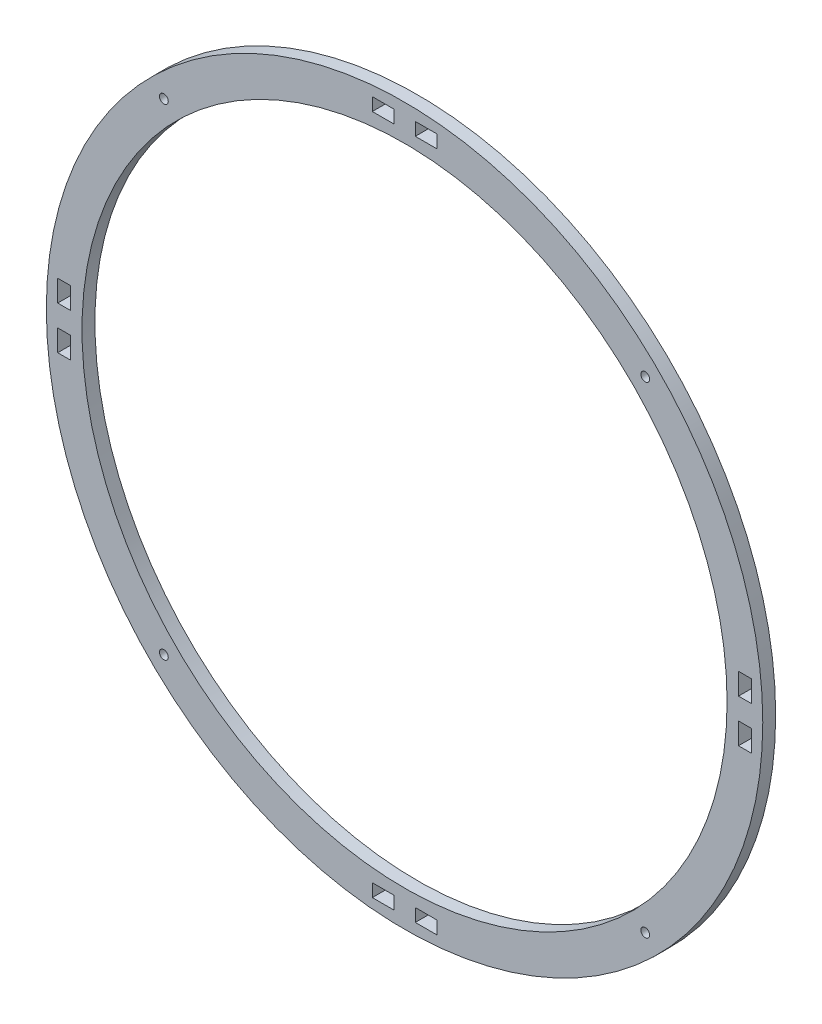
SolidWorks part; units mm, degrees
ref_plane "Alzado" through (0, 0, 0) normal (0, 0, 1) x (1, 0, 0)
ref_plane "Planta" through (0, 0, 0) normal (0, 1, 0) x (1, 0, 0)
ref_plane "Vista lateral" through (0, 0, 0) normal (1, 0, 0) x (0, 0, -1)
sketch "Croquis1" plane through (0, 0, 0) normal (0, 0, 1) x (1, 0, 0)
  line L0 (-44.7644, 42.1119) -> (355.2356, 42.1119)
  line L1 (355.2356, 42.1119) -> (355.2356, -357.8881)
  line L2 (355.2356, -357.8881) -> (-44.7644, -357.8881)
  line L3 (-44.7644, -357.8881) -> (-44.7644, 42.1119)
  line L4 (51.705, -49.341) -> (50.9394, -50.0625)
  circle A0 centre (154.1908, -158.8703) radius 150
  arc A1 (-0.0578, -95.9225) -> (308.4393, -95.9225) centre (154.1908, -158.8703) ccw
  arc A2 (267.7806, -36.9999) -> (40.601, -36.9999) centre (154.1908, -158.8703) ccw
  circle A3 centre (154.1908, -158.8703) radius 166.5985
  dimension "D1" = 400
  dimension "D2" = 400
extrude "Saliente-Extruir1" add sketch "Croquis1" along normal blind 6
sketch "Croquis2" plane through (0, 0, 6) normal (0, 0, 1) x (1, 0, 0)
  line L0 (154.1908, -8.8703) -> (154.1908, 7.7281)
  line L1 (154.1908, -308.8703) -> (154.1908, -325.4688)
  line L2 (304.1908, -158.8703) -> (320.7893, -158.8703)
  line L3 (4.1908, -158.8703) -> (-12.4077, -158.8703)
  line L4 (36.3879, -276.6733) -> (48.1248, -264.9364)
  line L5 (271.9937, -276.6733) -> (260.2568, -264.9364)
  line L6 (48.1248, -52.8043) -> (36.3879, -41.0674)
  line L7 (260.2568, -52.8043) -> (271.9937, -41.0674)
  line L8 (159.1908, 2.4289) -> (169.1908, 2.4289)
  line L9 (149.1908, 2.4289) -> (139.1908, 2.4289)
  line L10 (149.1908, -0.5711) -> (149.1908, 2.4289)
  line L11 (149.1908, -0.5711) -> (149.1908, -3.5711)
  line L12 (149.1908, -3.5711) -> (159.1908, -3.5711)
  line L13 (159.1908, -3.5711) -> (159.1908, 2.4289)
  line L14 (159.1908, 2.4289) -> (149.1908, 2.4289)
  line L15 (139.1908, 2.4289) -> (139.1908, -3.5711)
  line L16 (139.1908, -3.5711) -> (169.1908, -3.5711)
  line L17 (169.1908, -3.5711) -> (169.1908, 2.4289)
  line L18 (169.1908, -314.1696) -> (169.1908, -320.1696)
  line L19 (139.1908, -314.1696) -> (169.1908, -314.1696)
  line L20 (139.1908, -320.1696) -> (139.1908, -314.1696)
  line L21 (159.1908, -320.1696) -> (149.1908, -320.1696)
  line L22 (159.1908, -314.1696) -> (159.1908, -320.1696)
  line L23 (149.1908, -314.1696) -> (159.1908, -314.1696)
  line L24 (149.1908, -317.1696) -> (149.1908, -314.1696)
  line L25 (149.1908, -317.1696) -> (149.1908, -320.1696)
  line L26 (149.1908, -320.1696) -> (139.1908, -320.1696)
  line L27 (159.1908, -320.1696) -> (169.1908, -320.1696)
  line L28 (-4.1084, -158.8703) -> (-4.1084, -153.8703)
  line L29 (-4.1084, -158.8703) -> (-4.1084, -163.8703)
  line L30 (-4.1084, -163.8703) -> (-1.1084, -163.8703)
  line L31 (-4.1084, -163.8703) -> (-7.1084, -163.8703)
  line L32 (-7.1084, -163.8703) -> (-7.1084, -153.8703)
  line L33 (-7.1084, -153.8703) -> (-1.1084, -153.8703)
  line L34 (-1.1084, -153.8703) -> (-1.1084, -163.8703)
  line L35 (-1.1084, -163.8703) -> (-1.1084, -173.8703)
  line L36 (-1.1084, -173.8703) -> (-7.1084, -173.8703)
  line L37 (-7.1084, -173.8703) -> (-7.1084, -163.8703)
  line L38 (-7.1084, -153.8703) -> (-7.1084, -143.8703)
  line L39 (-7.1084, -143.8703) -> (-1.1084, -143.8703)
  line L40 (-1.1084, -143.8703) -> (-1.1084, -153.8703)
  line L41 (309.49, -143.8703) -> (309.49, -153.8703)
  line L42 (315.49, -143.8703) -> (309.49, -143.8703)
  line L43 (315.49, -153.8703) -> (315.49, -143.8703)
  line L44 (315.49, -173.8703) -> (315.49, -163.8703)
  line L45 (309.49, -173.8703) -> (315.49, -173.8703)
  line L46 (309.49, -163.8703) -> (309.49, -173.8703)
  line L47 (309.49, -153.8703) -> (309.49, -163.8703)
  line L48 (315.49, -153.8703) -> (309.49, -153.8703)
  line L49 (315.49, -163.8703) -> (315.49, -153.8703)
  line L50 (312.49, -163.8703) -> (315.49, -163.8703)
  line L51 (312.49, -163.8703) -> (309.49, -163.8703)
  line L52 (312.49, -158.8703) -> (312.49, -163.8703)
  line L53 (312.49, -158.8703) -> (312.49, -153.8703)
  circle A0 centre (154.1908, -158.8703) radius 150
  circle A1 centre (154.1908, -158.8703) radius 166.5985
  circle A2 centre (42.2563, -46.9359) radius 2.05
  circle A3 centre (266.1253, -46.9359) radius 2.05
  circle A4 centre (266.1253, -270.8048) radius 2.05
  circle A5 centre (42.2563, -270.8048) radius 2.05
  dimension "D5" = 45
  dimension "D8" = 45
extrude "Cortar-Extruir1" cut sketch "Croquis2" against normal blind 10 contours L15 L16 L11 L10 L9 | L16 L17 L8 L13 | L48 L43 L42 L41 | L50 L51 L46 L45 L44 | L22 L27 L18 L19 | L26 L25 L24 L19 L20 | L40 L39 L38 L33 | L37 L36 L35 L30 L31 | L6 A2 | L6 A2 | L7 A3 | L7 A3 | L5 A4 | L5 A4 | L4 A5 | L4 A5
